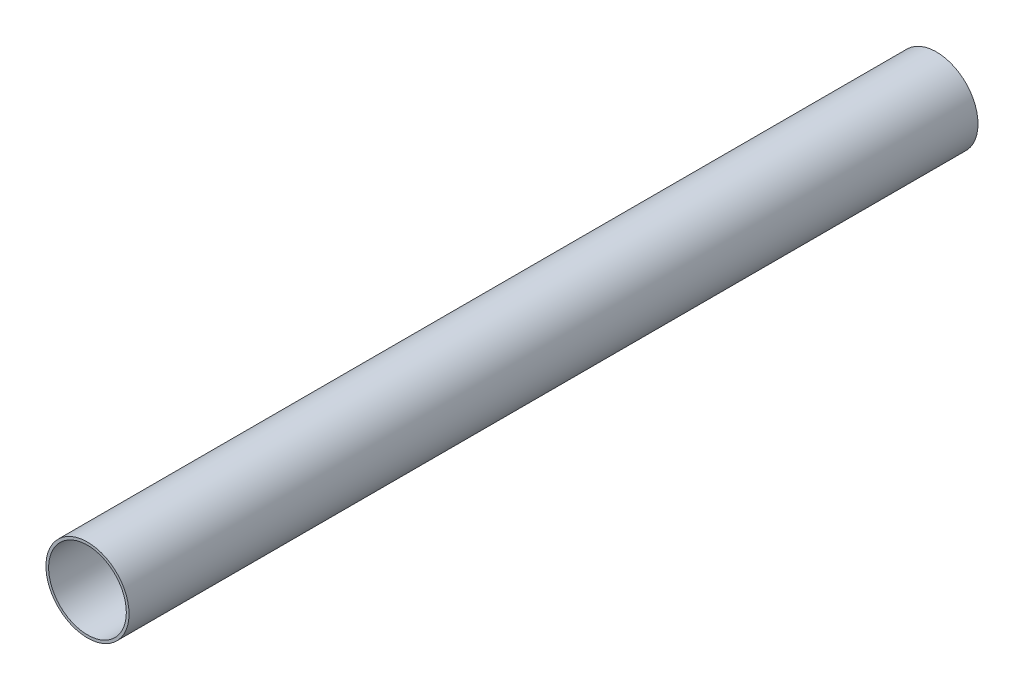
SolidWorks part; units mm, degrees
ref_plane "Front Plane" through (0, 0, 0) normal (0, 0, 1) x (1, 0, 0)
ref_plane "Top Plane" through (0, 0, 0) normal (0, 1, 0) x (1, 0, 0)
ref_plane "Right Plane" through (0, 0, 0) normal (1, 0, 0) x (0, 0, -1)
sketch "Sketch1" plane through (0, 0, 0) normal (0, 0, 1) x (1, 0, 0)
  circle A0 centre (0, 0) radius 49.2125
  circle A1 centre (0, 0) radius 46.0121
  dimension "D1" = 98.425
  dimension "D2" = 92.0242
extrude "Extrude1" add sketch "Sketch1" along normal blind 1005.332
